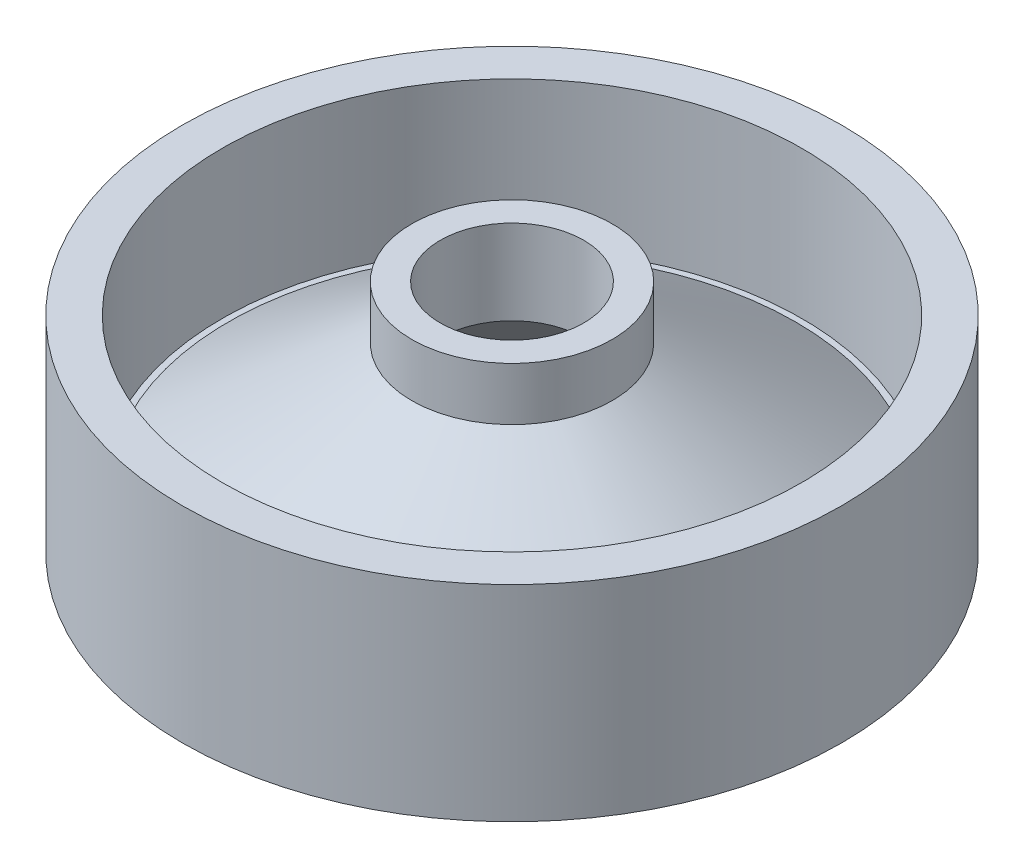
SolidWorks part; units mm, degrees
ref_plane "前视基准面" through (0, 0, 0) normal (0, 0, 1) x (1, 0, 0)
ref_plane "上视基准面" through (0, 0, 0) normal (0, 1, 0) x (1, 0, 0)
ref_plane "右视基准面" through (0, 0, 0) normal (1, 0, 0) x (0, 0, -1)
sketch "草图1" plane through (0, 0, 0) normal (0, 1, 0) x (1, 0, 0)
  circle A0 centre (0, 0) radius 11.38
  dimension "D1" = 22.76
extrude "凸台-拉伸1" add sketch "草图1" along normal blind 7.09 contours A0
sketch "草图2" plane through (0, 7.09, 0) normal (0, 1, 0) x (1, 0, 0)
  circle A0 centre (0, 0) radius 10
  dimension "D1" = 20
extrude "切除-拉伸1" cut sketch "草图2" against normal blind 5.09
sketch "草图3" plane through (0, 2, 0) normal (0, 1, 0) x (1, 0, 0)
  circle A0 centre (0, 0) radius 3.46
  dimension "D1" = 6.92
extrude "凸台-拉伸2" add sketch "草图3" along normal blind 6.1
ref_plane "基准面4" through (0, 6.27, 0) normal (0, 1, 0) x (1, 0, 0)
sketch "草图4" plane through (0, 6.27, 0) normal (0, 1, 0) x (1, 0, 0)
  circle A1 centre (0, 0) radius 3.46
  circle A2 centre (0, 0) radius 3.46
  dimension "D1" = 0
extrude "凸台-拉伸3" add sketch "草图4" against normal blind 5.18 draft 56 draft outward yes
sketch "草图5" plane through (0, 0, 0) normal (0, -1, 0) x (1, 0, 0)
  circle A0 centre (0, 0) radius 8.8731
  dimension "D1" = 17.7463
extrude "切除-拉伸2" cut sketch "草图5" against normal blind 5.18 draft 51
sketch "草图6" plane through (0, 5.18, 0) normal (0, -1, 0) x (1, 0, 0)
  circle A0 centre (0, 0) radius 2.4764
extrude "切除-拉伸3" cut sketch "草图6" against normal through all
